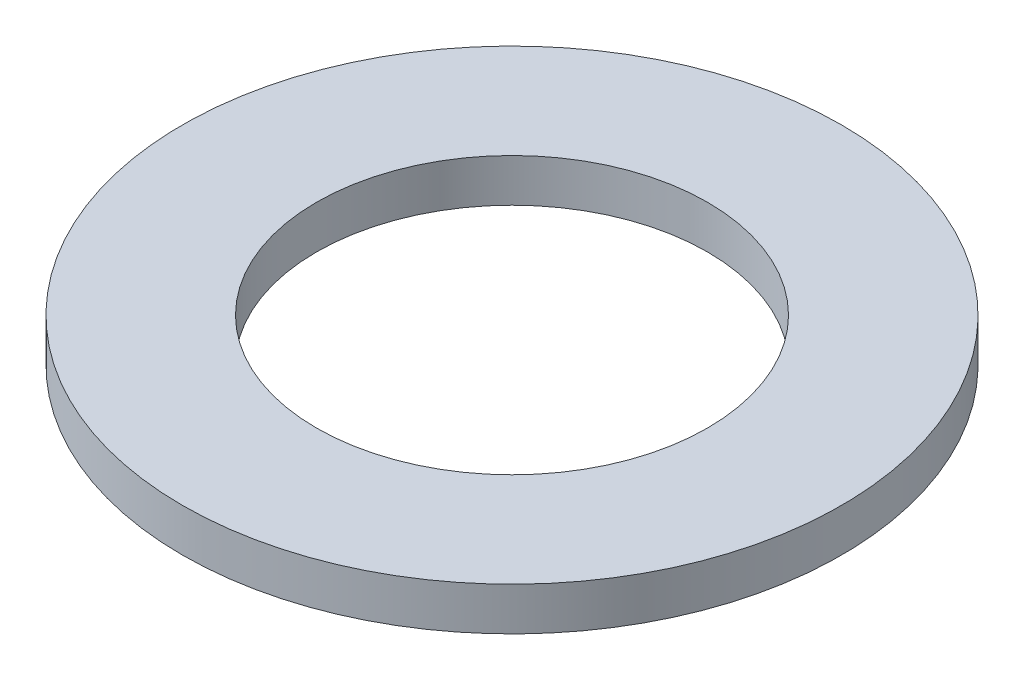
SolidWorks part; units mm, degrees
ref_plane "Front Plane" through (0, 0, 0) normal (0, 0, 1) x (1, 0, 0)
ref_plane "Top Plane" through (0, 0, 0) normal (0, 1, 0) x (1, 0, 0)
ref_plane "Right Plane" through (0, 0, 0) normal (1, 0, 0) x (0, 0, -1)
sketch "Sketch1" plane through (0, 0, 0) normal (0, 1, 0) x (1, 0, 0)
  circle A0 centre (0, 0) radius 19.05
  dimension "OD" = 38.1
extrude "Boss-Extrude1" add sketch "Sketch1" along normal blind 2.4892
sketch "Sketch5" plane through (0, 2.4892, 0) normal (0, 1, 0) x (-1, 0, 0)
  circle A0 centre (0, 0) radius 11.303
  dimension "ID" = 22.606
extrude "Cut-Extrude1" cut sketch "Sketch5" against normal through all
